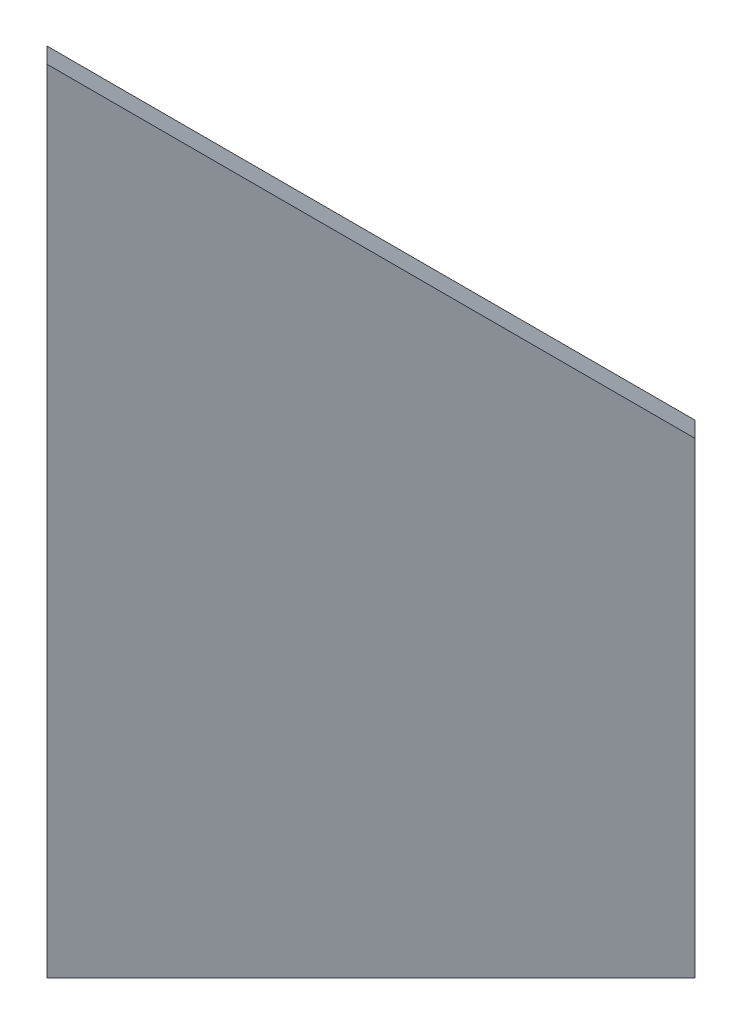
SolidWorks part; units mm, degrees
material "Acrylic (Medium-high impact)"
ref_plane "Front Plane" through (0, 0, 0) normal (0, 0, 1) x (1, 0, 0)
ref_plane "Top Plane" through (0, 0, 0) normal (0, 1, 0) x (1, 0, 0)
ref_plane "Right Plane" through (0, 0, 0) normal (1, 0, 0) x (0, 0, -1)
ref_plane "Plane1" through (80.4015, 0, 80.4015) normal (0.7071, 0, 0.7071) x (0.7071, 0, -0.7071)
sketch "Sketch1" plane through (80.4015, 0, 80.4015) normal (0.7071, 0, 0.7071) x (0.7071, 0, -0.7071)
  line L0 (-49.6381, -48.4129) -> (-111.1649, -4.9069) construction
  line L1 (-49.6381, -111.1649) -> (-49.6381, -48.4129) construction
  line L2 (-111.1649, -111.1649) -> (-49.6381, -111.1649) construction
  line L3 (-111.1649, -4.9069) -> (-111.1649, -111.1649) construction
  line L4 (-49.6381, -48.4129) -> (-111.1649, -4.9069)
  line L5 (-49.6381, -111.1649) -> (-49.6381, -48.4129)
  line L6 (-111.1649, -111.1649) -> (-49.6381, -111.1649)
  line L7 (-111.1649, -4.9069) -> (-111.1649, -111.1649)
extrude "Boss-Extrude1" add sketch "Sketch1" along normal mid plane 3
